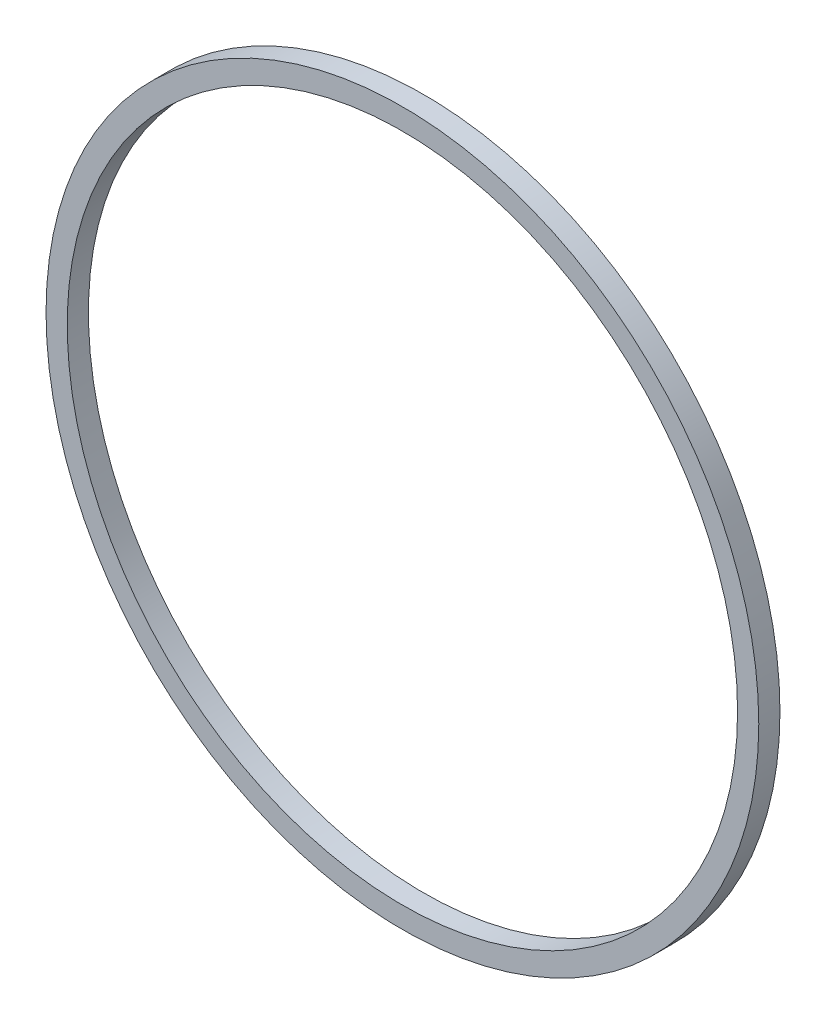
SolidWorks part; units mm, degrees
ref_plane "Front Plane" through (0, 0, 0) normal (0, 0, 1) x (1, 0, 0)
ref_plane "Top Plane" through (0, 0, 0) normal (0, 1, 0) x (1, 0, 0)
ref_plane "Right Plane" through (0, 0, 0) normal (1, 0, 0) x (0, 0, -1)
sketch "Sketch1" plane through (0, 0, 0) normal (0, 0, 1) x (1, 0, 0)
  circle A0 centre (0, 0) radius 26.162
  circle A1 centre (0, 0) radius 24.6063
  dimension "D1" = 52.324
  dimension "D2" = 1.5557
extrude "Boss-Extrude1" add sketch "Sketch1" along normal blind 1.5557
